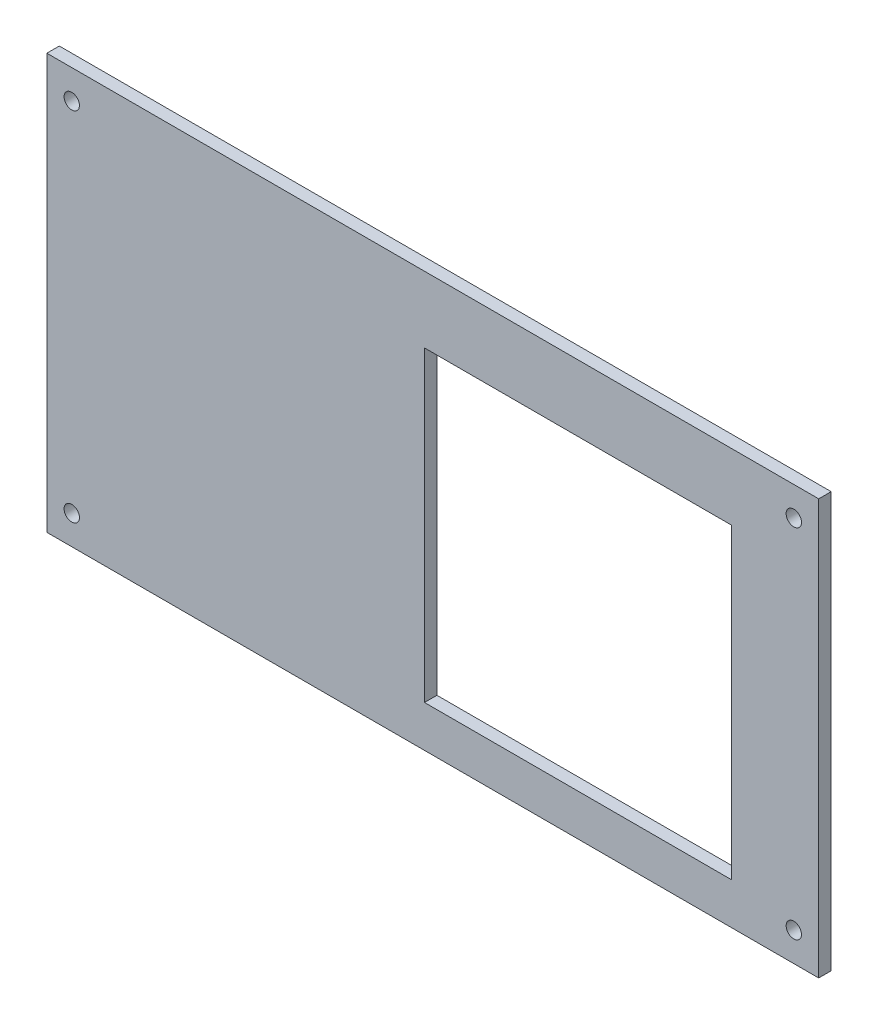
SolidWorks part; units mm, degrees
material "PMMA laser cult panels"
ref_plane "Front Plane" through (0, 0, 0) normal (0, 0, 1) x (1, 0, 0)
ref_plane "Top Plane" through (0, 0, 0) normal (0, 1, 0) x (1, 0, 0)
ref_plane "Right Plane" through (0, 0, 0) normal (1, 0, 0) x (0, 0, -1)
sketch "Sketch1" plane through (0, 0, 0) normal (0, 0, 1) x (1, 0, 0)
  line L1 (0, 0) -> (186, 0)
  line L2 (0, 0) -> (0, 100)
  line L3 (0, 100) -> (186, 100)
  line L4 (186, 0) -> (186, 100)
  dimension "D1" = 186
  dimension "D2" = 100
extrude "Boss-Extrude1" add sketch "Sketch1" along normal blind 3
sketch "Sketch2" plane through (0, 0, 0) normal (0, 0, -1) x (-1, 0, 0)
  line L0 (-186, 0) -> (-186, 100) construction
  line L1 (-180, 7) -> (-6, 7)
  line L2 (-180, 7) -> (-180, 93)
  line L3 (-180, 93) -> (-6, 93)
  line L4 (-6, 7) -> (-6, 93)
  line L5 (0, 100) -> (0, 0) construction
  line L6 (-186, 100) -> (0, 100) construction
  line L7 (0, 0) -> (-186, 0) construction
  line L9 (-165, 10) -> (-91, 10)
  line L10 (-165, 10) -> (-165, 84)
  line L11 (-165, 84) -> (-91, 84)
  line L12 (-91, 10) -> (-91, 84)
  circle A0 centre (-180, 7) radius 1.85
  circle A1 centre (-180, 93) radius 1.85
  circle A2 centre (-6, 93) radius 1.85
  circle A3 centre (-6, 7) radius 1.85
  dimension "D5" = 3.7
  dimension "D1" = 6
  dimension "D2" = 6
  dimension "D3" = 7
  dimension "D4" = 7
  dimension "D6" = 16
  dimension "D7" = 91
  dimension "D8" = 10
  dimension "D9" = 21
extrude "Cut-Extrude1" cut sketch "Sketch2" against normal through all contours L9 L12 L11 L10 | A0 | A1 | A3 | A2
